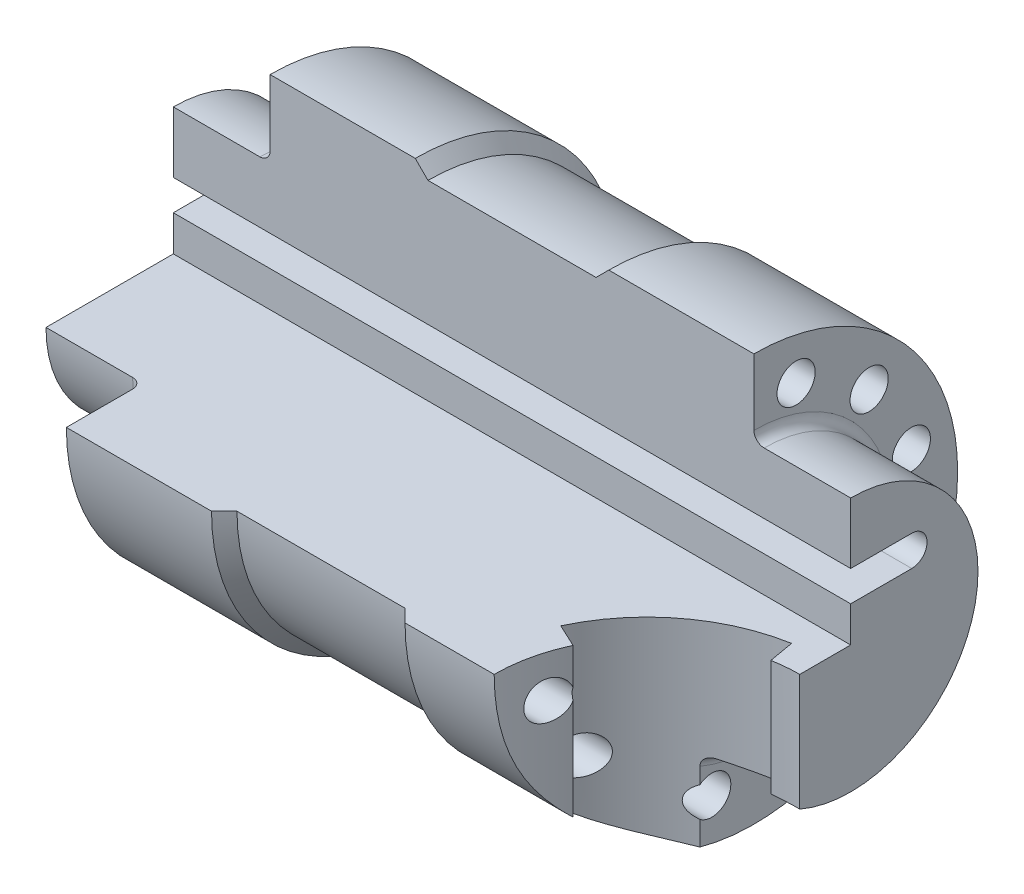
SolidWorks part; units mm, degrees
material "AISI 1020"
ref_plane "Płaszczyzna przednia" through (0, 0, 0) normal (0, 0, 1) x (1, 0, 0)
ref_plane "Płaszczyzna górna" through (0, 0, 0) normal (0, 1, 0) x (1, 0, 0)
ref_plane "Płaszczyzna prawa" through (0, 0, 0) normal (1, 0, 0) x (0, 0, -1)
sketch "Szkic2" plane through (0, 0, 0) normal (0, 0, 1) x (1, 0, 0)
  line L0 (0, 0) -> (0, 25)
  line L1 (0, 25) -> (19, 25)
  line L2 (19, 25) -> (19, 40)
  line L3 (19, 40) -> (47.5, 40)
  line L4 (47.5, 40) -> (50, 37.5)
  line L5 (50, 37.5) -> (83, 37.5)
  line L6 (83, 37.5) -> (85.5, 40)
  line L7 (85.5, 40) -> (114, 40)
  line L8 (114, 40) -> (114, 25)
  line L9 (114, 25) -> (133, 25)
  line L10 (133, 25) -> (133, 0)
  line L11 (133, 0) -> (0, 0)
  dimension "D1" = 25
  dimension "D2" = 40
  dimension "D3" = 135
  dimension "D4" = 135
  dimension "D5" = 19
  dimension "D6" = 28.5
  dimension "D7" = 133
  dimension "D8" = 19
  dimension "D9" = 2.5
revolve "Obrót1" add sketch "Szkic2" angle 360 about L11
fillet "Zaokrąglenie1" radius 2 2 edges at (19, 25, 0) (114, 25, 0)
sketch "Szkic3" plane through (0, 0, 0) normal (-1, 0, 0) x (0, 0, 1)
  line L0 (0, 0) -> (0, 7)
  line L1 (0, 7) -> (-12, 7)
  line L2 (-12, 13) -> (0, 13)
  line L3 (0, 13) -> (0, 40)
  line L4 (40, 0) -> (0, 0)
  arc A0 (-12, 7) -> (-12, 13) centre (-12, 10) cw
  circle A1 centre (0, 0) radius 40 construction
  arc A2 (0, 40) -> (40, 0) centre (0, 0) cw
  dimension "D2" = 3
  dimension "D1" = 12
  dimension "D3" = 7
extrude "Wytnij-wyciągnięcie1" cut sketch "Szkic3" against normal through all
sketch "Szkic4" plane through (19, 0, 0) normal (-1, 0, 0) x (0, 0, 1)
  line L1 (0, 0) -> (-8.2822, 30.9096) construction
  line L2 (0, 40) -> (0, 27) construction
  circle A0 centre (-8.2822, 30.9096) radius 3.75
  dimension "D1" = 32
  dimension "D3" = 7.5
  dimension "D2" = 15
extrude "Wytnij-wyciągnięcie2" cut sketch "Szkic4" against normal through all
pattern_circular "Szyk kołowy1" count 9 every 30 about axis through (0, 0, 0) along (1, 0, 0) of "Wytnij-wyciągnięcie2"
sketch "Szkic5" plane through (0, 0, 0) normal (0, 1, 0) x (1, 0, 0)
  line L0 (133, -25) -> (133, -47.4625) construction
  line L1 (114, -40) -> (142.7394, -40) construction
  line L2 (105.8108, -27.3215) -> (101.2792, -25.2084) construction
  line L3 (133, -40) -> (127.9993, -11.6394) construction
  line L4 (133, 0) -> (133, -25) construction
  line L5 (114, -40) -> (85.5, -40) construction
  line L6 (101.2792, -25.2084) -> (105.8108, -27.3215)
  line L7 (126.9223, -5.5317) -> (127.7906, -10.4558)
  line L8 (126.7725, -4.6822) -> (126.4839, -3.0454) construction
  line L9 (127.7906, -10.4558) -> (126.9223, -5.5317) construction
  arc A1 (126.9223, -5.5317) -> (101.2792, -25.2084) centre (133, -40) ccw
  arc A2 (105.8108, -27.3215) -> (127.7906, -10.4558) centre (133, -40) ccw
  dimension "D1" = 70
  dimension "D2" = 60
  dimension "D5" = 5
  dimension "D3" = 10
  dimension "D4" = 25
extrude "Wytnij-wyciągnięcie3" cut sketch "Szkic5" against normal through all
sketch "Szkic6" plane through (0, 0, 0) normal (-1, 0, 0) x (0, 0, 1)
  line L0 (-19.8997, 3) -> (-5, 3)
  line L1 (-4, 2) -> (-4, -3)
  line L2 (-3, -4) -> (19.3649, -4)
  line L3 (0, 7) -> (0, 0) construction
  line L4 (-12, 7) -> (0, 7) construction
  line L5 (0, 0) -> (25, 0) construction
  arc A0 (20.3332, -5.25) -> (-20.8947, 2.1) centre (0, 0) cw
  arc A1 (0, 25) -> (25, 0) centre (0, 0) ccw construction
  arc A2 (-5, 3) -> (-4, 2) centre (-5, 2) cw
  arc A3 (-20.8947, 2.1) -> (-19.8997, 3) centre (-19.8997, 2) cw
  arc A4 (-4, -3) -> (-3, -4) centre (-3, -3) ccw
  arc A5 (19.3649, -4) -> (20.3332, -5.25) centre (19.3649, -5) cw
  dimension "D1" = 4
  dimension "D5" = 1
  dimension "D6" = 1
  dimension "D7" = 1
  dimension "D8" = 1
  dimension "D2" = 4
  dimension "D3" = 4
  dimension "D4" = 4
extrude "Wytnij-wyciągnięcie4" cut sketch "Szkic6" against normal blind 10 contours A0 A3 L0 A2 L1 A4 L2 A5
fillet "Zaokrąglenie2" radius 1 8 edges at (10, -20.674, -3.6857) (10, 3, -12.4499) (10, -0.5, -4) (10, -4, 8.1825) (10, 2.7416, -20.5706) (10, 2.7071, -4.2929) (10, -3.7071, -3.7071) (10, -4.3876, 20.1555)
fillet "Zaokrąglenie3" radius 1 8 edges at (0, -0.5, -4) (0, -4, 8.1825) (0, -20.674, -3.6857) (0, 3, -12.4499) (0, 2.7416, -20.5706) (0, -4.3876, 20.1555) (0, -3.7071, -3.7071) (0, 2.7071, -4.2929)
equation "\"B\" = 19"
equation "\"C\" = 28.5"
equation "\"A\"= 133"
